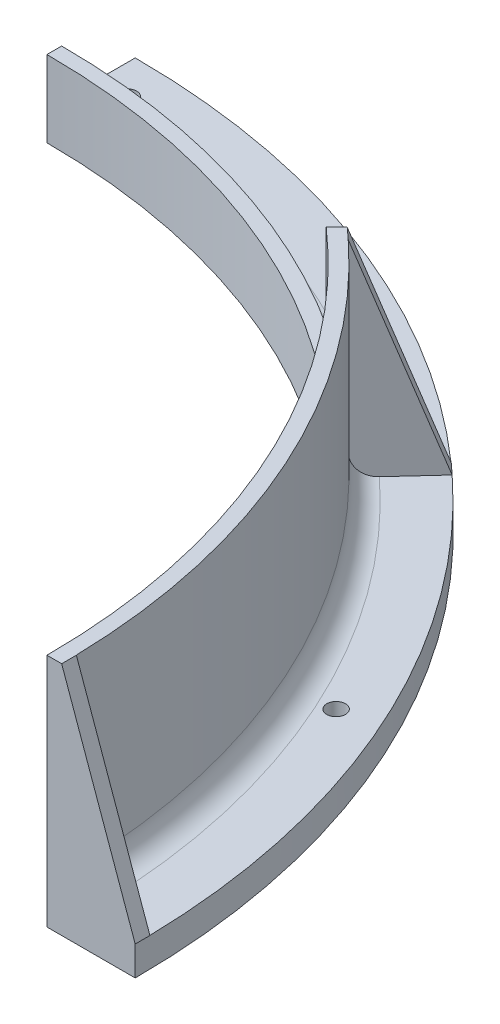
SolidWorks part; units mm, degrees
material "PET"
ref_plane "Front" through (0, 0, 0) normal (0, 0, 1) x (1, 0, 0)
ref_plane "Top" through (0, 0, 0) normal (0, 1, 0) x (1, 0, 0)
ref_plane "Right" through (0, 0, 0) normal (1, 0, 0) x (0, 0, -1)
sketch "Sketch1" plane through (0, 0, 0) normal (0, 1, 0) x (1, 0, 0)
  line L0 (165.608, 0) -> (146.558, 0)
  line L1 (0, -165.608) -> (0, -146.558)
  arc A0 (0, -165.608) -> (165.608, 0) centre (0, 0) ccw
  arc A1 (0, -146.558) -> (146.558, 0) centre (0, 0) ccw
  dimension "D1" = 146.558
  dimension "D2" = 19.05
extrude "Boss-Extrude1" add sketch "Sketch1" along normal blind 6.35
sketch "Sketch2" plane through (0, 6.35, 0) normal (0, 1, 0) x (1, 0, 0)
  line L0 (165.608, 0) -> (146.558, 0) construction
  line L2 (146.558, 0) -> (149.733, 0)
  line L3 (0, -146.558) -> (0, -149.733)
  arc A0 (0, -146.558) -> (146.558, 0) centre (0, 0) ccw
  arc A1 (0, -149.733) -> (149.733, 0) centre (0, 0) ccw
  dimension "D1" = 3.175
extrude "Boss-Extrude2" add sketch "Sketch2" along normal blind 44.45
sketch "Sketch3" plane through (0, 50.8, 0) normal (0, 1, 0) x (1, 0, 0)
  line L0 (96.6779, -110.1483) -> (98.9276, -112.398)
  line L1 (0, -146.558) -> (0, -149.733)
  line L2 (103.6322, -103.6322) -> (105.8772, -105.8772) construction
  arc A0 (0, -146.558) -> (146.558, 0) centre (0, 0) ccw construction
  arc A1 (0, -149.733) -> (149.733, 0) centre (0, 0) ccw construction
  arc A2 (98.9276, -112.398) -> (0, -149.733) centre (0, 0) cw
  arc A3 (0, -146.558) -> (96.6779, -110.1483) centre (0, 0) ccw
  arc A4 (0, -149.733) -> (149.733, 0) centre (0, 0) ccw construction
  dimension "D1" = 9.525
extrude "Cut-Extrude1" cut sketch "Sketch3" against normal offset from surface (34.29 mm away) 10.16 up to face at (95.1626, 6.35, 95.1626)
sketch "Sketch8" plane through (0, 6.35, 0) normal (0, 1, 0) x (1, 0, 0)
  line L0 (0, -149.733) -> (0, -165.608) construction
  line L1 (6.35, -157.5426) -> (87.8583, -130.9233) construction
  line L2 (87.8583, -130.9233) -> (143.383, -65.5843) construction
  circle A0 centre (0, 0) radius 157.6705 construction
  point P0 (6.35, -157.5426)
  point P2 (87.8583, -130.9233)
  point P4 (143.383, -65.5843)
  point P13 (0, -157.6705)
  dimension "D1" = 6.35
  dimension "D2" = 85.7449
hole_wizard "#10-32 Tapped Hole1" positions "Sketch8" profile "Sketch7" tap size "#10-32" standard "ANSI Inch" end condition up to next
sketch "Sketch7" plane through (6.35, 6.35, 157.5426) normal (1, 0, 0) x (0, 0, 1)
  line L0 (0, 0) -> (0, 6.35)
  line L1 (0, 6.35) -> (2.0193, 6.35)
  line L2 (2.0193, 6.35) -> (2.0193, 0)
  line L5 (2.0193, 0) -> (0, 0)
  line L11 (0, -6.35) -> (0, 107.95) construction
  dimension "Thru Tap Drill Dia." = 4.0386
  dimension "Thru Tap Drill Depth" = 6.35
cosmetic thread "Hole Thread1" [suppressed] parameters "D1"=6.35, "D2"=5.0386
cosmetic thread "Hole Thread2" [suppressed] parameters "D1"=6.35, "D2"=5.0386
cosmetic thread "Hole Thread3" [suppressed] parameters "D1"=6.35, "D2"=5.0386
sketch "Sketch9" plane through (0, 0, 0) normal (0, 0, -1) x (-1, 0, 0)
  line L0 (-165.608, 6.35) -> (-149.733, 50.8)
  line L1 (-149.733, 50.8) -> (-146.558, 50.8)
  line L2 (-146.558, 50.8) -> (-146.558, 6.35)
  line L3 (-146.558, 50.8) -> (-146.558, 0) construction
  line L4 (-146.558, 6.35) -> (-165.608, 6.35)
extrude "Boss-Extrude3" add sketch "Sketch9" against normal blind 3.175
pattern_circular "CirPattern1" count 2 every 47.375 about axis through (0, 0, 0) along (0, 1, 0) of "Boss-Extrude3"
fillet "Fillet1" radius 4.7625 2 edges at (136.4725, 6.35, 61.6054) (52.9391, 6.35, 140.0622)
mirror "Mirror1" about plane through (0, 0, 0) normal (0, 0, 1) of bodies 116 113
cosmetic thread "Hole Thread4" [suppressed] parameters "D1"=6.35, "D2"=5.0386
cosmetic thread "Hole Thread5" [suppressed] parameters "D1"=6.35, "D2"=5.0386
cosmetic thread "Hole Thread6" [suppressed] parameters "D1"=6.35, "D2"=5.0386
delete or keep bodies "Body-Delete/Keep 1" type delete bodies bodies 116
